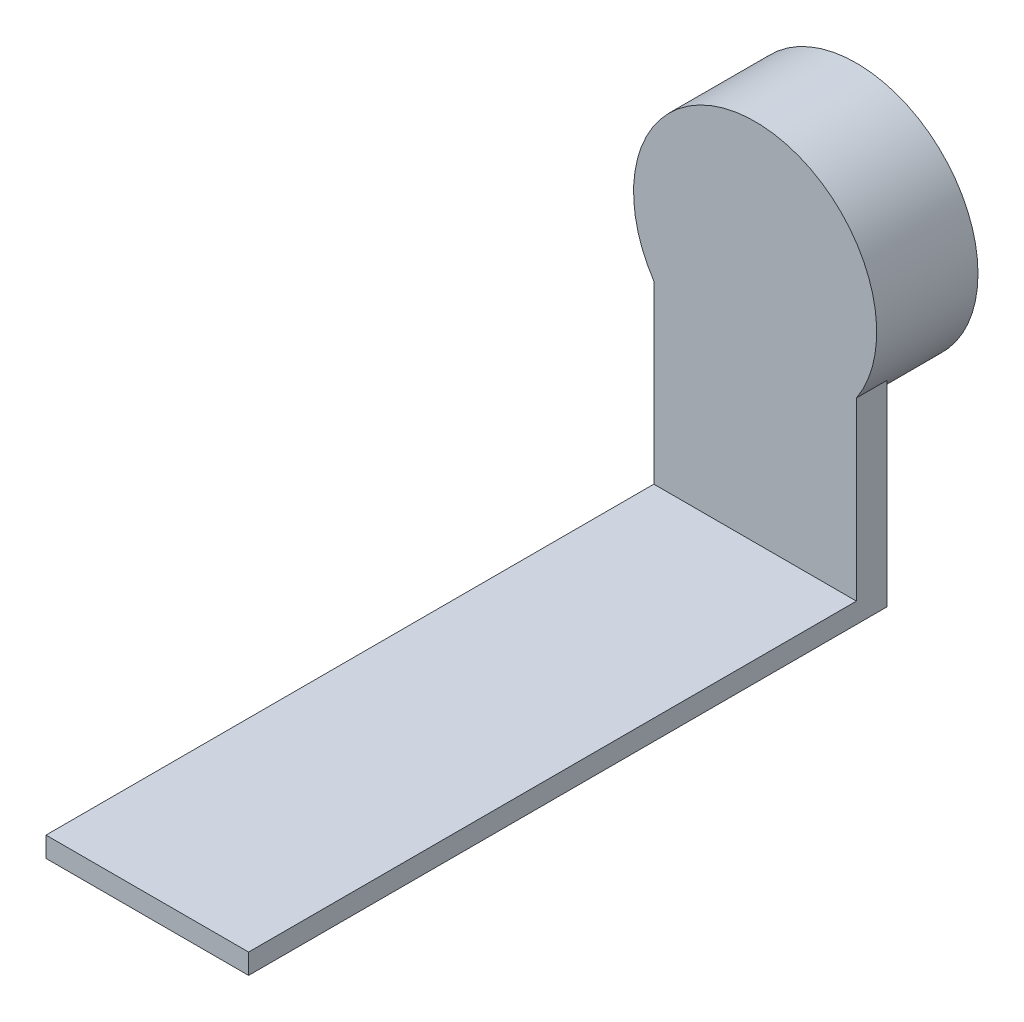
SolidWorks part; units mm, degrees
ref_plane "Front Plane" through (0, 0, 0) normal (0, 0, 1) x (1, 0, 0)
ref_plane "Top Plane" through (0, 0, 0) normal (0, 1, 0) x (1, 0, 0)
ref_plane "Right Plane" through (0, 0, 0) normal (1, 0, 0) x (0, 0, -1)
sketch "Sketch2" plane through (0, 0, 0) normal (0, 0, 1) x (1, 0, 0)
  line L0 (10, -6.6332) -> (10, -26)
  line L3 (10, -26) -> (-10, -26)
  line L7 (-10, -6.6332) -> (-10, -26)
  circle A0 centre (0, 0) radius 12
  dimension "D1" = 26
  dimension "D2" = 10
  dimension "D4" = 24
  dimension "D3" = 10
extrude "Boss-Extrude1" add sketch "Sketch2" along normal blind 10 contours A0
sketch "Sketch3" plane through (0, 0, 10) normal (0, 0, 1) x (1, 0, 0)
  line L0 (-10, -26) -> (-10, -6.6332)
  line L3 (10, -26) -> (-10, -26)
  line L7 (10, -26) -> (10, -6.6332)
  circle A0 centre (0, 0) radius 12 construction
  arc A1 (-10, -6.6332) -> (10, -6.6332) centre (0, 0) ccw
  point P0 (0, 0)
  dimension "D1" = 26
  dimension "D2" = 10
  dimension "D3" = 10
extrude "Boss-Extrude2" add sketch "Sketch3" against normal blind 3
sketch "Sketch4" plane through (0, 0, 10) normal (0, 0, 1) x (1, 0, 0)
  line L0 (10, -26) -> (10, -6.6332) construction
  line L1 (-10, -26) -> (10, -26)
  line L2 (-10, -26) -> (-10, -24)
  line L3 (-10, -24) -> (10, -24)
  line L4 (10, -26) -> (10, -24)
extrude "Boss-Extrude3" add sketch "Sketch4" along normal blind 60
sketch "Sketch5" plane through (0, 0, 0) normal (0, 0, -1) x (-1, 0, 0)
  circle A0 centre (0, 0) radius 10
extrude "Cut-Extrude1" cut sketch "Sketch5" against normal blind 8
